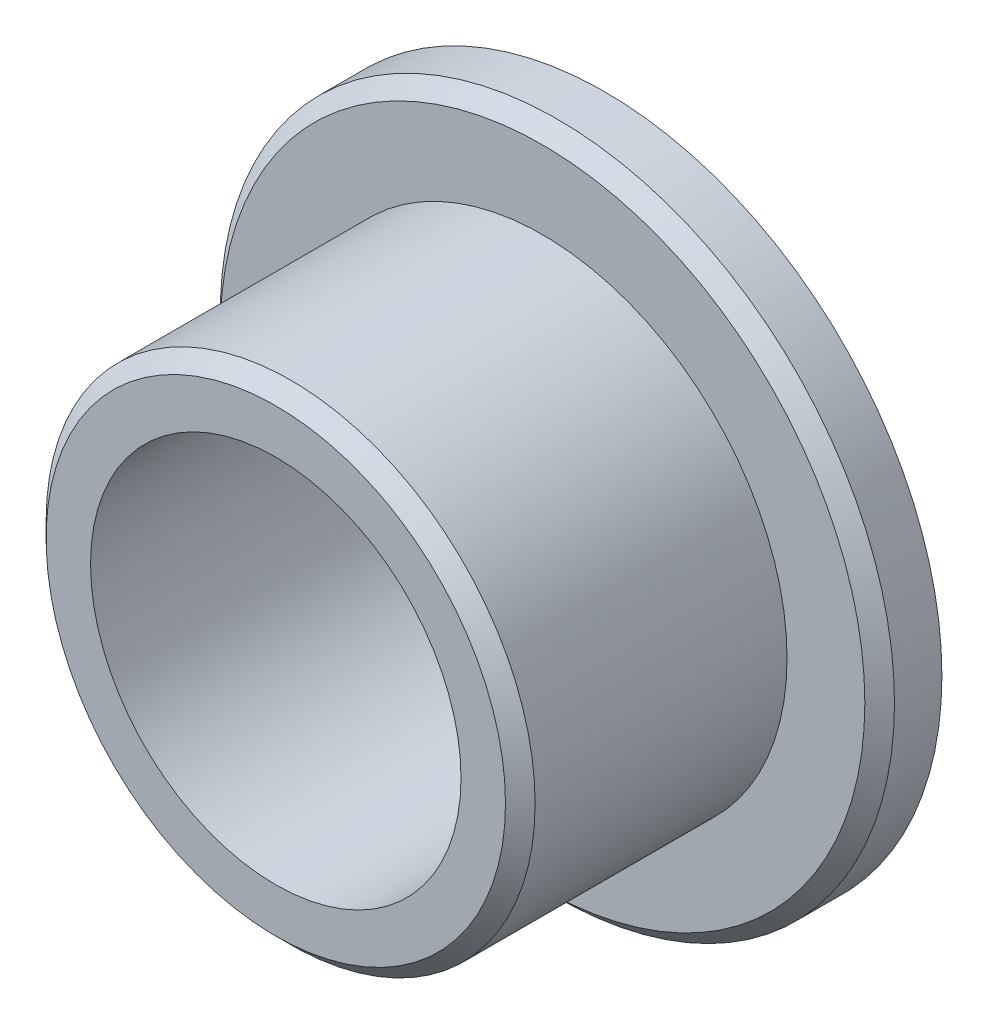
SolidWorks part; units mm, degrees
ref_plane "前视基准面" through (0, 0, 0) normal (0, 0, 1) x (1, 0, 0)
ref_plane "上视基准面" through (0, 0, 0) normal (0, 1, 0) x (1, 0, 0)
ref_plane "右视基准面" through (0, 0, 0) normal (1, 0, 0) x (0, 0, -1)
sketch "草图1" plane through (0, 0, 0) normal (0, 0, 1) x (1, 0, 0)
  circle A0 centre (0, 0) radius 22.75
  dimension "D1" = 45.5
extrude "凸台-拉伸1" add sketch "草图1" along normal blind 4.2
sketch "草图2" plane through (0, 0, 4.2) normal (0, 0, 1) x (1, 0, 0)
  circle A0 centre (0, 0) radius 16.5
  dimension "D1" = 33
extrude "凸台-拉伸2" add sketch "草图2" along normal blind 18
sketch "草图3" plane through (0, 0, 22.2) normal (0, 0, 1) x (1, 0, 0)
  circle A0 centre (0, 0) radius 12.5
  dimension "D1" = 25
extrude "切除-拉伸1" cut sketch "草图3" against normal through all
chamfer "倒角1" distance 1 angle 45 2 edges at (22.75, 0, 4.2) (16.5, 0, 22.2)
